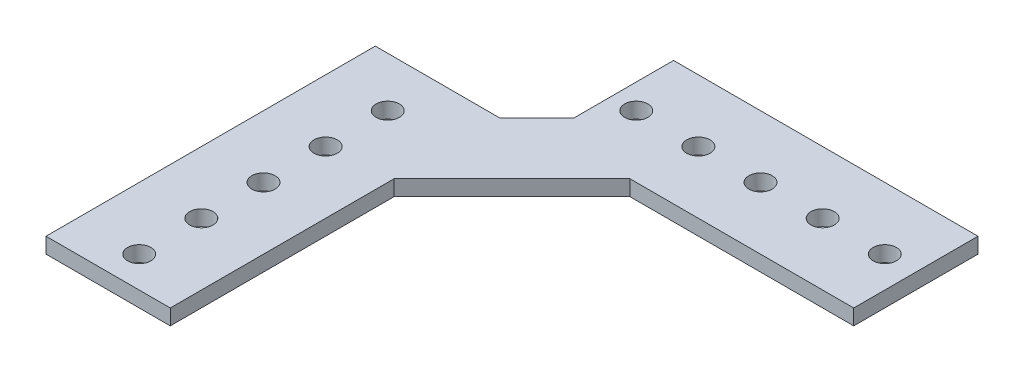
SolidWorks part; units mm, degrees
ref_plane "Front Plane" through (0, 0, 0) normal (0, 0, 1) x (1, 0, 0)
ref_plane "Top Plane" through (0, 0, 0) normal (0, 1, 0) x (1, 0, 0)
ref_plane "Right Plane" through (0, 0, 0) normal (1, 0, 0) x (0, 0, -1)
sketch "Sketch1" plane through (0, 0, 0) normal (0, 1, 0) x (1, 0, 0)
  line L13 (0, 67.31) -> (25.4, 67.31)
  line L14 (0, 67.31) -> (0, 0)
  line L17 (33.02, 95.25) -> (95.25, 95.25)
  line L18 (33.02, 95.25) -> (33.02, 74.93)
  line L20 (95.25, 95.25) -> (95.25, 69.85)
  line L23 (49.4926, 69.85) -> (95.25, 69.85)
  line L24 (25.4, 67.31) -> (33.02, 74.93)
  line L25 (25.4, 45.7574) -> (49.4926, 69.85)
  line L26 (25.4, 0) -> (25.4, 45.7574)
  line L29 (0, 0) -> (25.4, 0)
  circle A2 centre (38.1, 82.55) radius 2.3812
  circle A5 centre (12.7, 57.15) radius 2.3812
  circle A6 centre (50.8, 82.55) radius 2.3812
  circle A7 centre (63.5, 82.55) radius 2.3812
  circle A8 centre (76.2, 82.55) radius 2.3813
  circle A9 centre (88.9, 82.55) radius 2.3812
  circle A10 centre (12.7, 44.45) radius 2.3812
  circle A11 centre (12.7, 31.75) radius 2.3812
  circle A12 centre (12.7, 19.05) radius 2.3812
  circle A13 centre (12.7, 6.35) radius 2.3812
  point P3 (12.7, 67.31)
  point P5 (95.25, 82.55)
  point P7 (12.7, 0)
  dimension "D5" = 7.62
  dimension "D21" = 15.24
  dimension "D17" = 4.7625
  dimension "D9" = 12.7
  dimension "D3" = 95.25
  dimension "D4" = 135
  dimension "D6" = 95.25
  dimension "D7" = 45.7574
  dimension "D8" = 5.08
  dimension "D10" = 25.4
  dimension "D11" = 12.7
  dimension "D19" = 10.16
extrude "Boss-Extrude1" add sketch "Sketch1" along normal blind 3.175 contours L14 L29 L26 L25 L23 L20 L17 L18 L24 L13 A13 A12 A11 A10 A9 A8 A7 A6 A5 A2
